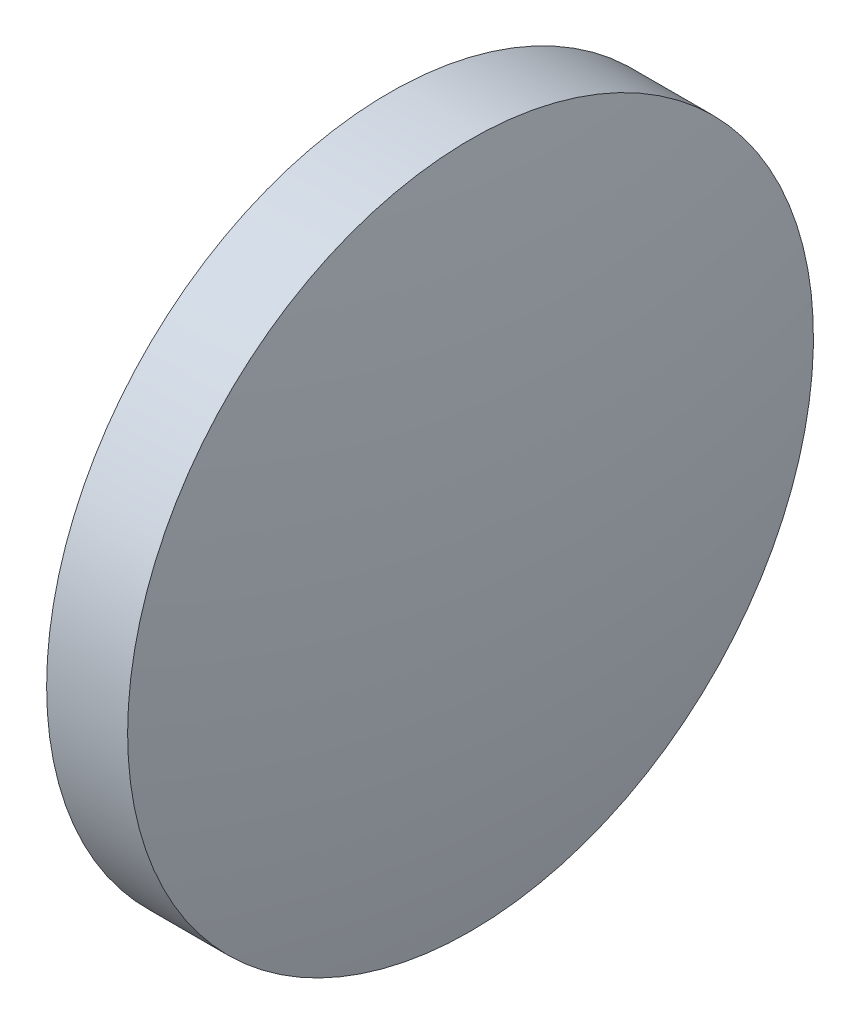
SolidWorks part; units mm, degrees
ref_plane "前视基准面" through (0, 0, 0) normal (0, 0, 1) x (1, 0, 0)
ref_plane "上视基准面" through (0, 0, 0) normal (0, 1, 0) x (1, 0, 0)
ref_plane "右视基准面" through (0, 0, 0) normal (1, 0, 0) x (0, 0, -1)
sketch "草图1" plane through (0, 0, 0) normal (0, 0, 1) x (1, 0, 0)
  line L0 (110.1654, 65.2336) -> (128.9614, 65.2336) construction
  line L1 (115.7736, 65.2336) -> (115.7736, 77.9336)
  line L2 (115.7736, 77.9336) -> (118.7732, 77.9336)
  line L3 (119.9546, 65.2336) -> (115.7736, 65.2336)
  arc A0 (119.9546, 65.2336) -> (118.7732, 77.9336) centre (51.1046, 65.2336) ccw
  dimension "D1" = 68.85
  dimension "D2" = 4.181
revolve "旋转1" add sketch "草图1" angle 360 about L0
